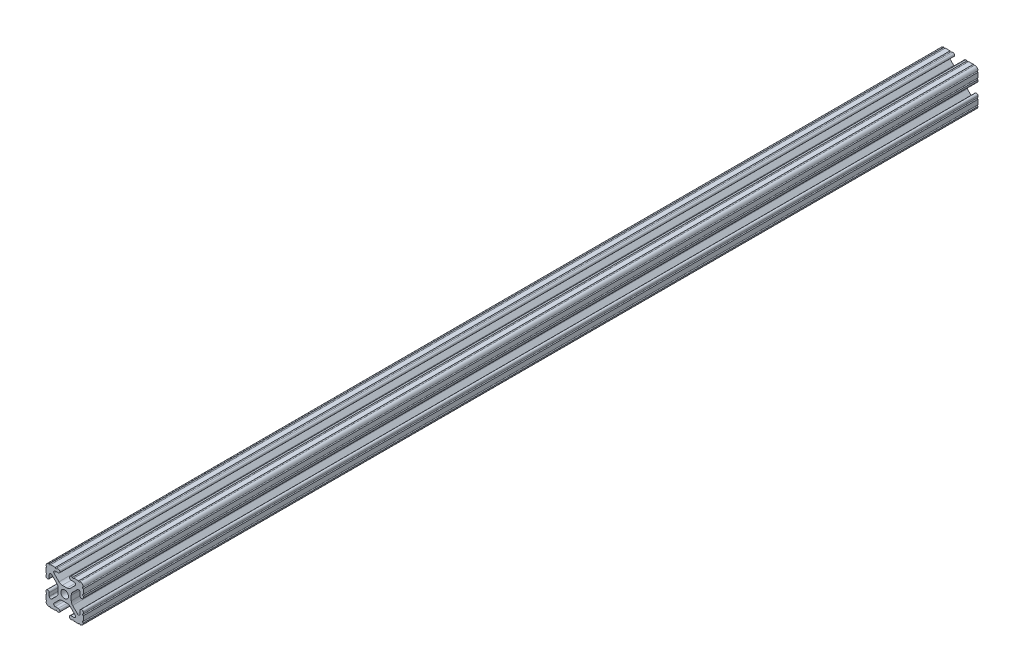
SolidWorks part; units mm, degrees
ref_plane "Front Plane" through (0, 0, 0) normal (0, 0, 1) x (1, 0, 0)
ref_plane "Top Plane" through (0, 0, 0) normal (0, 1, 0) x (1, 0, 0)
ref_plane "Right Plane" through (0, 0, 0) normal (1, 0, 0) x (0, 0, -1)
ref_plane "Plane1" through (0, 0, -304.8) normal (0, 0, -1) x (-1, 0, 0)
sketch "Sketch1" plane through (0, 0, -304.8) normal (0, 0, -1) x (-1, 0, 0)
  line L0 (12.7, -9.5504) -> (12.7, -6.3331)
  line L1 (12.7, -5.3171) -> (12.7, -4.3434)
  line L2 (10.4902, -4.3434) -> (10.4902, -6.4748)
  line L3 (8.7558, -7.1932) -> (5.4257, -3.8632)
  line L4 (4.4958, -1.6181) -> (4.4958, 1.6181)
  line L5 (5.4257, 3.8632) -> (8.7558, 7.1932)
  line L6 (10.4902, 6.4748) -> (10.4902, 4.3434)
  line L7 (12.7, 4.3434) -> (12.7, 5.3171)
  line L8 (12.7, 6.3331) -> (12.7, 9.5504)
  line L9 (9.5504, 12.7) -> (6.3331, 12.7)
  line L10 (5.3171, 12.7) -> (4.3434, 12.7)
  line L11 (4.3434, 10.4902) -> (6.4748, 10.4902)
  line L12 (7.1932, 8.7558) -> (3.8632, 5.4257)
  line L13 (1.6181, 4.4958) -> (-1.6181, 4.4958)
  line L14 (-3.8632, 5.4257) -> (-7.1932, 8.7558)
  line L15 (-6.4748, 10.4902) -> (-4.3434, 10.4902)
  line L16 (-4.3434, 12.7) -> (-5.3171, 12.7)
  line L17 (-6.3331, 12.7) -> (-9.5504, 12.7)
  line L18 (-12.7, 9.5504) -> (-12.7, 6.3331)
  line L19 (-12.7, 5.3171) -> (-12.7, 4.3434)
  line L20 (-10.4902, 4.3434) -> (-10.4902, 6.4748)
  line L21 (-8.7558, 7.1932) -> (-5.4257, 3.8632)
  line L22 (-4.4958, 1.6181) -> (-4.4958, -1.6181)
  line L23 (-5.4257, -3.8632) -> (-8.7558, -7.1932)
  line L24 (-10.4902, -6.4748) -> (-10.4902, -4.3434)
  line L25 (-12.7, -4.3434) -> (-12.7, -5.3171)
  line L26 (-12.7, -6.3331) -> (-12.7, -9.5504)
  line L27 (-9.5504, -12.7) -> (-6.3331, -12.7)
  line L28 (-5.3171, -12.7) -> (-4.3434, -12.7)
  line L29 (-4.3434, -10.4902) -> (-6.4748, -10.4902)
  line L30 (-7.1932, -8.7558) -> (-3.8632, -5.4257)
  line L31 (-1.6181, -4.4958) -> (1.6181, -4.4958)
  line L32 (3.8632, -5.4257) -> (7.1932, -8.7558)
  line L33 (6.4748, -10.4902) -> (4.3434, -10.4902)
  line L34 (4.3434, -12.7) -> (5.3171, -12.7)
  line L35 (6.3331, -12.7) -> (9.5504, -12.7)
  arc A0 (12.6998, -10.5664) -> (12.7, -9.5504) centre (12.7, -10.0584) cw
  arc A1 (12.7, -6.3331) -> (12.7, -5.3171) centre (12.7, -5.8251) cw
  arc A2 (12.7, -4.3434) -> (10.4902, -4.3434) centre (11.5951, -4.3434) ccw
  arc A3 (10.4902, -6.4748) -> (8.7558, -7.1932) centre (9.4742, -6.4748) cw
  arc A4 (5.4257, -3.8632) -> (4.4958, -1.6181) centre (7.6708, -1.6181) cw
  arc A5 (4.4958, 1.6181) -> (5.4257, 3.8632) centre (7.6708, 1.6181) cw
  arc A6 (8.7558, 7.1932) -> (10.4902, 6.4748) centre (9.4742, 6.4748) cw
  arc A7 (10.4902, 4.3434) -> (12.7, 4.3434) centre (11.5951, 4.3434) ccw
  arc A8 (12.7, 5.3171) -> (12.7, 6.3331) centre (12.7, 5.8251) cw
  arc A9 (12.7, 9.5504) -> (12.6998, 10.5664) centre (12.7, 10.0584) cw
  arc A10 (12.6998, 10.5664) -> (10.5664, 12.6998) centre (10.5918, 10.5918) ccw
  arc A11 (10.5664, 12.6998) -> (9.5504, 12.7) centre (10.0584, 12.7) cw
  arc A12 (6.3331, 12.7) -> (5.3171, 12.7) centre (5.8251, 12.7) cw
  arc A13 (4.3434, 12.7) -> (4.3434, 10.4902) centre (4.3434, 11.5951) ccw
  arc A14 (6.4748, 10.4902) -> (7.1932, 8.7558) centre (6.4748, 9.4742) cw
  arc A15 (3.8632, 5.4257) -> (1.6181, 4.4958) centre (1.6181, 7.6708) cw
  arc A16 (-1.6181, 4.4958) -> (-3.8632, 5.4257) centre (-1.6181, 7.6708) cw
  arc A17 (-7.1932, 8.7558) -> (-6.4748, 10.4902) centre (-6.4748, 9.4742) cw
  arc A18 (-4.3434, 10.4902) -> (-4.3434, 12.7) centre (-4.3434, 11.5951) ccw
  arc A19 (-5.3171, 12.7) -> (-6.3331, 12.7) centre (-5.8251, 12.7) cw
  arc A20 (-9.5504, 12.7) -> (-10.5664, 12.6998) centre (-10.0584, 12.7) cw
  arc A21 (-10.5664, 12.6998) -> (-12.6998, 10.5664) centre (-10.5918, 10.5918) ccw
  arc A22 (-12.6998, 10.5664) -> (-12.7, 9.5504) centre (-12.7, 10.0584) cw
  arc A23 (-12.7, 6.3331) -> (-12.7, 5.3171) centre (-12.7, 5.8251) cw
  arc A24 (-12.7, 4.3434) -> (-10.4902, 4.3434) centre (-11.5951, 4.3434) ccw
  arc A25 (-10.4902, 6.4748) -> (-8.7558, 7.1932) centre (-9.4742, 6.4748) cw
  arc A26 (-5.4257, 3.8632) -> (-4.4958, 1.6181) centre (-7.6708, 1.6181) cw
  arc A27 (-4.4958, -1.6181) -> (-5.4257, -3.8632) centre (-7.6708, -1.6181) cw
  arc A28 (-8.7558, -7.1932) -> (-10.4902, -6.4748) centre (-9.4742, -6.4748) cw
  arc A29 (-10.4902, -4.3434) -> (-12.7, -4.3434) centre (-11.5951, -4.3434) ccw
  arc A30 (-12.7, -5.3171) -> (-12.7, -6.3331) centre (-12.7, -5.8251) cw
  arc A31 (-12.7, -9.5504) -> (-12.6998, -10.5664) centre (-12.7, -10.0584) cw
  arc A32 (-12.6998, -10.5664) -> (-10.5664, -12.6998) centre (-10.5918, -10.5918) ccw
  arc A33 (-10.5664, -12.6998) -> (-9.5504, -12.7) centre (-10.0584, -12.7) cw
  arc A34 (-6.3331, -12.7) -> (-5.3171, -12.7) centre (-5.8251, -12.7) cw
  arc A35 (-4.3434, -12.7) -> (-4.3434, -10.4902) centre (-4.3434, -11.5951) ccw
  arc A36 (-6.4748, -10.4902) -> (-7.1932, -8.7558) centre (-6.4748, -9.4742) cw
  arc A37 (-3.8632, -5.4257) -> (-1.6181, -4.4958) centre (-1.6181, -7.6708) cw
  arc A38 (1.6181, -4.4958) -> (3.8632, -5.4257) centre (1.6181, -7.6708) cw
  arc A39 (7.1932, -8.7558) -> (6.4748, -10.4902) centre (6.4748, -9.4742) cw
  arc A40 (4.3434, -10.4902) -> (4.3434, -12.7) centre (4.3434, -11.5951) ccw
  arc A41 (5.3171, -12.7) -> (6.3331, -12.7) centre (5.8251, -12.7) cw
  arc A42 (9.5504, -12.7) -> (10.5664, -12.6998) centre (10.0584, -12.7) cw
  arc A43 (10.5664, -12.6998) -> (12.6998, -10.5664) centre (10.5918, -10.5918) ccw
  circle A44 centre (0, 0) radius 2.6035
extrude "Boss-Extrude1" add sketch "Sketch1" against normal blind 609.6
